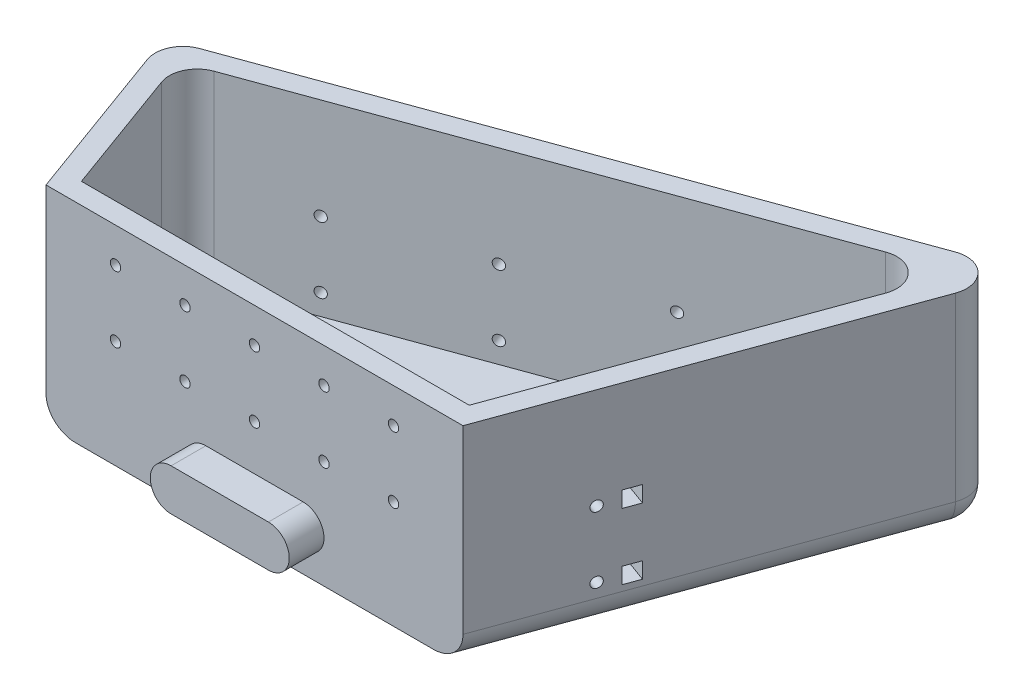
SolidWorks part; units mm, degrees
ref_plane "Front Plane" through (0, 0, 0) normal (0, 0, 1) x (1, 0, 0)
ref_plane "Top Plane" through (0, 0, 0) normal (0, 1, 0) x (1, 0, 0)
ref_plane "Right Plane" through (0, 0, 0) normal (1, 0, 0) x (0, 0, -1)
sketch "Sketch1" plane through (0, 0, 0) normal (0, 1, 0) x (1, 0, 0)
  line L0 (14.6239, -62.0657) -> (4.9135, -35.3866)
  line L1 (4.9135, -35.3866) -> (96.4621, -2.0657)
  line L2 (96.4621, -2.0657) -> (74.6239, -62.0657)
  line L3 (74.6239, -62.0657) -> (14.6239, -62.0657)
  line L4 (16.7245, -59.0657) -> (8.7587, -37.1796)
  line L5 (8.7587, -37.1796) -> (91.4426, -7.0851)
  line L6 (91.4426, -7.0851) -> (72.5233, -59.0657)
  line L7 (72.5233, -59.0657) -> (16.7245, -59.0657)
  line L8 (12.7416, -48.1227) -> (9.9225, -49.1487) construction
  line L9 (50.1007, -22.1324) -> (49.0746, -19.3133) construction
  line L10 (81.983, -33.0754) -> (84.802, -34.1015) construction
  line L11 (44.6239, -59.0657) -> (44.6239, -62.0657) construction
  dimension "D1" = 3
  dimension "D2" = 110
  dimension "D3" = 110
  dimension "D4" = 60
  dimension "D5" = 60
  dimension "D6" = 50
extrude "Boss-Extrude1" add sketch "Sketch1" along normal blind 30
sketch "Sketch3" plane through (0, 0, 0) normal (0, 1, 0) x (1, 0, 0)
  line L0 (8.7587, -37.1796) -> (16.7245, -59.0657)
  line L1 (16.7245, -59.0657) -> (72.5233, -59.0657)
  line L2 (72.5233, -59.0657) -> (91.4426, -7.0851)
  line L3 (91.4426, -7.0851) -> (8.7587, -37.1796)
extrude "Boss-Extrude2" add sketch "Sketch3" along normal blind 3
fillet "Fillet1" radius 4 7 edges at (96.4621, 15, 2.0657) (91.4426, 16.5, 7.0851) (8.7587, 16.5, 37.1796) (4.9135, 15, 35.3866) (9.7687, 0, 48.7261) (85.543, 0, 32.0657) (50.6878, 0, 18.7261)
sketch "Sketch4" plane through (11.9478, 0, 32.8264) normal (-0.342, 0, -0.9397) x (-0.9397, 0, 0.342)
  line L0 (-81.3602, 30) -> (-81.3602, 4) construction
  line L1 (-81.3602, 15.5) -> (3.4857, 15.5) construction
  line L2 (-81.3602, 15.5) -> (-81.3602, 6) construction
  line L3 (-81.3602, 6) -> (3.4857, 6) construction
  line L4 (3.4857, 15.5) -> (3.4857, 6) construction
  line L5 (3.4857, 4) -> (3.4857, 30) construction
  line L7 (-71.5143, 15.5) -> (-71.5143, 6) construction
  line L8 (-51.5143, 15.5) -> (-51.5143, 6) construction
  line L9 (-31.5143, 15.5) -> (-31.5143, 6) construction
  line L10 (-11.5143, 15.5) -> (-11.5143, 6) construction
  line L11 (-81.3602, 4) -> (3.4857, 4) construction
  circle A0 centre (-71.5143, 15.5) radius 0.75
  circle A1 centre (-51.5143, 15.5) radius 0.75
  circle A2 centre (-31.5143, 15.5) radius 0.75
  circle A3 centre (-11.5143, 15.5) radius 0.75
  circle A4 centre (-11.5143, 6) radius 0.75
  circle A5 centre (-31.5143, 6) radius 0.75
  circle A6 centre (-51.5143, 6) radius 0.75
  circle A7 centre (-71.5143, 6) radius 0.75
  dimension "D3" = 1.5
  dimension "D1" = 9.5
  dimension "D2" = 2
  dimension "D4" = 20
  dimension "D5" = 20
  dimension "D6" = 20
  dimension "D7" = 15
extrude "Cut-Extrude1" cut sketch "Sketch4" against normal blind 3
sketch "Sketch6" plane through (0, 0, 62.0657) normal (0, 0, 1) x (1, 0, 0)
  line L0 (14.6239, 25) -> (74.6239, 25) construction
  line L1 (14.6239, 30) -> (14.6239, 4) construction
  line L2 (74.6239, 30) -> (74.6239, 4) construction
  line L3 (14.6239, 15.5) -> (74.6239, 15.5) construction
  line L4 (14.6239, 30) -> (74.6239, 30) construction
  line L5 (34.6239, 25) -> (34.6239, 15.5) construction
  line L6 (44.6239, 25) -> (44.6239, 15.5) construction
  line L7 (54.6239, 25) -> (54.6239, 15.5) construction
  line L8 (64.6239, 25) -> (64.6239, 15.5) construction
  line L9 (24.6239, 25) -> (24.6239, 15.5) construction
  circle A0 centre (34.6239, 25) radius 0.75
  circle A1 centre (44.6239, 25) radius 0.75
  circle A2 centre (54.6239, 25) radius 0.75
  circle A3 centre (64.6239, 25) radius 0.75
  circle A4 centre (34.6239, 15.5) radius 0.75
  circle A5 centre (44.6239, 15.5) radius 0.75
  circle A6 centre (54.6239, 15.5) radius 0.75
  circle A7 centre (64.6239, 15.5) radius 0.75
  circle A8 centre (24.6239, 25) radius 0.75
  circle A9 centre (24.6239, 15.5) radius 0.75
  dimension "D3" = 10
  dimension "D8" = 1.5
  dimension "D1" = 9.5
  dimension "D2" = 5
  dimension "D4" = 10
  dimension "D5" = 10
  dimension "D6" = 10
  dimension "D7" = 10
sketch "Sketch9" plane through (85.8421, 0, 31.244) normal (0.9397, 0, 0.342) x (0.342, 0, -0.9397)
  line L0 (-32.7998, 15.5) -> (22.4729, 15.5) construction
  line L1 (-32.7998, 30) -> (-32.7998, 4) construction
  line L2 (22.4729, 4) -> (22.4729, 30) construction
  line L3 (-32.7998, 6) -> (22.4729, 6) construction
  line L4 (-32.7998, 4) -> (22.4729, 4) construction
  line L5 (-17.7998, 15.5) -> (-17.7998, 6) construction
  circle A0 centre (-17.7998, 15.5) radius 0.75
  circle A1 centre (-17.7998, 6) radius 0.75
  dimension "D3" = 1.5
  dimension "D1" = 9.5
  dimension "D2" = 2
  dimension "D4" = 15
extrude "Cut-Extrude4" cut sketch "Sketch9" against normal blind 3
extrude "Cut-Extrude3" cut sketch "Sketch6" against normal blind 3
sketch "Sketch7" plane through (0, 0, 62.0657) normal (0, 0, 1) x (1, 0, 0)
  line L0 (37.6239, 6) -> (51.6239, 6) construction
  line L1 (37.6239, 9) -> (51.6239, 9)
  line L2 (37.6239, 3) -> (51.6239, 3)
  line L3 (18.8806, 0) -> (70.3672, 0) construction
  line L4 (34.6239, 6) -> (14.6239, 6) construction
  line L5 (14.6239, 30) -> (14.6239, 4) construction
  line L6 (54.6239, 6) -> (74.6239, 6) construction
  line L7 (74.6239, 30) -> (74.6239, 4) construction
  arc A0 (37.6239, 9) -> (37.6239, 3) centre (37.6239, 6) ccw
  arc A1 (51.6239, 3) -> (51.6239, 9) centre (51.6239, 6) ccw
  point P2 (44.6239, 6)
  point P7 (54.6239, 6)
  point P8 (34.6239, 6)
  dimension "D1" = 6
  dimension "D2" = 20
  dimension "D3" = 6
extrude "Boss-Extrude3" add sketch "Sketch7" along normal blind 5
sketch "Sketch10" plane through (85.8421, 0, 31.244) normal (0.9397, 0, 0.342) x (0.342, 0, -0.9397)
  line L0 (-17.7998, 15.5) -> (-13.7998, 15.5) construction
  line L1 (-13.7998, 15.5) -> (-13.7998, 6) construction
  line L2 (-13.7998, 6) -> (-17.7998, 6) construction
  line L4 (-14.9498, 16.65) -> (-12.6498, 16.65)
  line L5 (-14.9498, 16.65) -> (-14.9498, 14.35)
  line L6 (-14.9498, 14.35) -> (-12.6498, 14.35)
  line L7 (-12.6498, 16.65) -> (-12.6498, 14.35)
  line L8 (-14.9498, 16.65) -> (-12.6498, 14.35) construction
  line L9 (-14.9498, 14.35) -> (-12.6498, 16.65) construction
  line L10 (-14.9498, 7.15) -> (-12.6498, 7.15)
  line L11 (-14.9498, 7.15) -> (-14.9498, 4.85)
  line L12 (-14.9498, 4.85) -> (-12.6498, 4.85)
  line L13 (-12.6498, 7.15) -> (-12.6498, 4.85)
  line L14 (-14.9498, 7.15) -> (-12.6498, 4.85) construction
  line L15 (-14.9498, 4.85) -> (-12.6498, 7.15) construction
  circle A0 centre (-17.7998, 6) radius 0.75 construction
  circle A1 centre (-17.7998, 15.5) radius 0.75 construction
  dimension "D1" = 4
  dimension "D2" = 2.3
  dimension "D3" = 2.3
  dimension "D4" = 2.3
  dimension "D5" = 2.3
extrude "Cut-Extrude5" cut sketch "Sketch10" against normal blind 3
